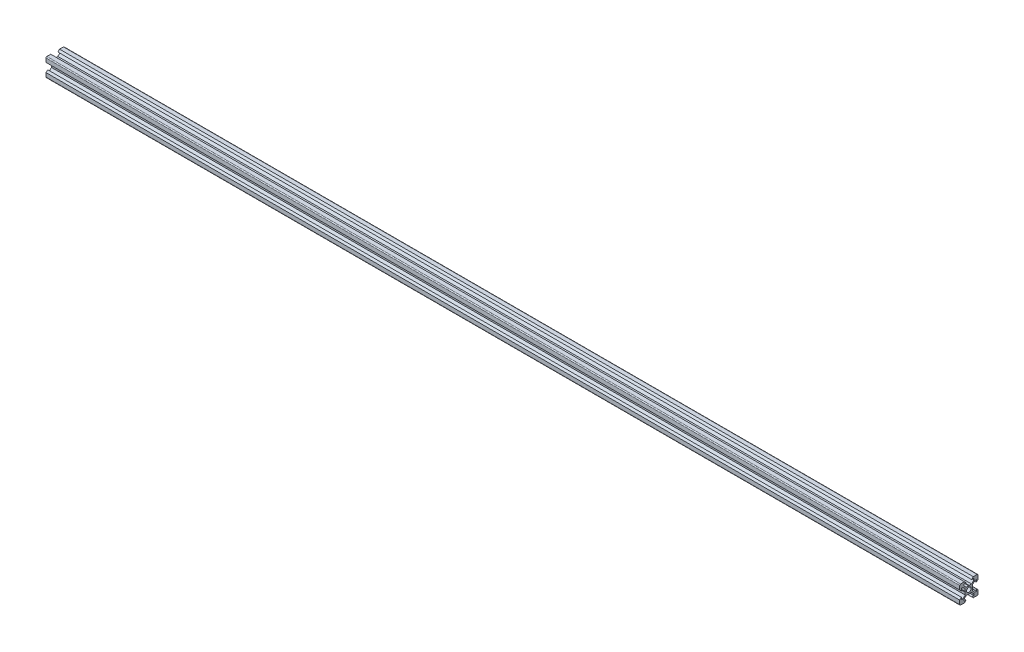
SolidWorks part; units mm, degrees
material "6063-T5"
material "6063-T5"
ref_plane "Plano frontal" through (0, 0, 0) normal (0, 0, 1) x (1, 0, 0)
ref_plane "Plano superior" through (0, 0, 0) normal (0, 1, 0) x (1, 0, 0)
ref_plane "Plano direito" through (0, 0, 0) normal (1, 0, 0) x (0, 0, -1)
sketch "Esboço1" plane through (0, 0, 0) normal (0, 0, 1) x (1, 0, 0)
  line L0 (0, 0) -> (1000, 0)
  dimension "D1" = 1000
other "Quadrado PF20-11 - PERFIL 2020 V-SLOT(1)"
ref_plane "Plano1" through (0, 0, 0) normal (1, 0, 0) x (0, 1, 0)
sketch "Sketch11" plane through (0, 0, 0) normal (1, 0, 0) x (0, 1, 0)
  line L0 (-4.8, 10) -> (-3, 8.2)
  line L1 (-3, 8.2) -> (-5.5, 8.2)
  line L2 (-5.5, 8.2) -> (-5.5, 6.5607)
  line L3 (-5.5, 6.5607) -> (-2.9393, 4)
  line L4 (-2.9393, 4) -> (-0.3, 4)
  line L5 (5.5, 6.5607) -> (2.9393, 4)
  line L6 (5.5, 8.2) -> (5.5, 6.5607)
  line L7 (3, 8.2) -> (5.5, 8.2)
  line L8 (4.8, 10) -> (3, 8.2)
  line L9 (-0.3, 4) -> (0, 3.7)
  line L10 (0.3, 4) -> (0, 3.7)
  line L11 (0.3, 4) -> (2.9393, 4)
  line L12 (9, 10) -> (4.8, 10)
  line L13 (10, 4.8) -> (8.2, 3)
  line L14 (10, 4.8) -> (10, 9)
  line L15 (8.2, 3) -> (8.2, 5.5)
  line L16 (8.2, 5.5) -> (6.5607, 5.5)
  line L17 (6.5607, 5.5) -> (4, 2.9393)
  line L18 (4.8, -10) -> (3, -8.2)
  line L19 (3, -8.2) -> (5.5, -8.2)
  line L20 (5.5, -8.2) -> (5.5, -6.5607)
  line L21 (5.5, -6.5607) -> (2.9393, -4)
  line L22 (2.9393, -4) -> (0.3, -4)
  line L23 (0.3, -4) -> (0, -3.7)
  line L24 (-0.3, -4) -> (0, -3.7)
  line L25 (-0.3, -4) -> (-2.9393, -4)
  line L26 (-5.5, -6.5607) -> (-2.9393, -4)
  line L27 (-5.5, -8.2) -> (-5.5, -6.5607)
  line L28 (-3, -8.2) -> (-5.5, -8.2)
  line L29 (-4.8, -10) -> (-3, -8.2)
  line L30 (-10, -4.8) -> (-10, -9)
  line L31 (-10, -4.8) -> (-8.2, -3)
  line L32 (-8.2, -3) -> (-8.2, -5.5)
  line L33 (-8.2, -5.5) -> (-6.5607, -5.5)
  line L34 (-6.5607, -5.5) -> (-4, -2.9393)
  line L35 (-4, -2.9393) -> (-4, -0.3)
  line L36 (-4, -0.3) -> (-3.7, 0)
  line L37 (-4, 0.3) -> (-3.7, 0)
  line L38 (-4, 0.3) -> (-4, 2.9393)
  line L39 (-6.5607, 5.5) -> (-4, 2.9393)
  line L40 (-8.2, 5.5) -> (-6.5607, 5.5)
  line L41 (-8.2, 3) -> (-8.2, 5.5)
  line L42 (-10, 4.8) -> (-8.2, 3)
  line L43 (-4.8, 10) -> (-9, 10)
  line L44 (4, 2.9393) -> (4, 0.3)
  line L45 (4, 0.3) -> (3.7, 0)
  line L46 (4, -0.3) -> (3.7, 0)
  line L47 (4, -0.3) -> (4, -2.9393)
  line L48 (6.5607, -5.5) -> (4, -2.9393)
  line L49 (8.2, -5.5) -> (6.5607, -5.5)
  line L50 (8.2, -3) -> (8.2, -5.5)
  line L51 (10, -4.8) -> (8.2, -3)
  line L52 (10, -9) -> (10, -4.8)
  line L53 (4.8, -10) -> (9, -10)
  line L106 (-10, 9) -> (-10, 4.8)
  line L107 (-9, -10) -> (-4.8, -10)
  arc A0 (10, 9) -> (9, 10) centre (9, 9) ccw
  arc A1 (9, -10) -> (10, -9) centre (9, -9) ccw
  arc A3 (-10, -9) -> (-9, -10) centre (-9, -9) ccw
  arc A4 (-9, 10) -> (-10, 9) centre (-9, 9) ccw
  circle A7 centre (0, 0) radius 2.5
  point P1 (-10, 10)
  point P3 (10, 10)
  point P4 (10, -10)
  point P68 (0, 0)
  point P70 (10, 0)
  point P71 (0, 0)
  point P72 (0, 0)
  point P113 (0, -10)
  point P114 (-10, -10)
  point P115 (-10, 0)
  point P116 (0, 10)
  point P118 (0, 0)
